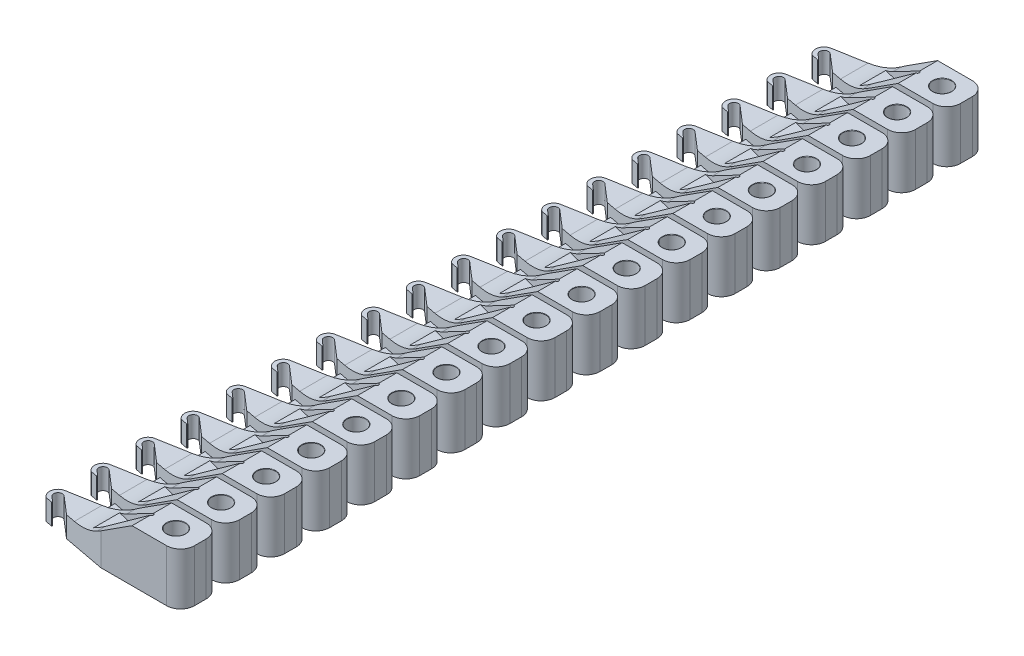
SolidWorks part; units mm, degrees
ref_plane "Front Plane" through (0, 0, 0) normal (0, 0, 1) x (1, 0, 0)
ref_plane "Top Plane" through (0, 0, 0) normal (0, 1, 0) x (1, 0, 0)
ref_plane "Right Plane" through (0, 0, 0) normal (1, 0, 0) x (0, 0, -1)
sketch "Sketch1" plane through (0, 0, 0) normal (0, 1, 0) x (1, 0, 0)
  line L0 (0.7, 0.57) -> (-1.6, 0.57)
  line L1 (0.7, 0.57) -> (0.7, -0.57)
  line L2 (0.7, -0.57) -> (-1.6, -0.57)
  line L3 (-1.6, 0.57) -> (-3.681, 0.2)
  line L4 (-3.4049, 0) -> (-2.2666, -0.982) construction
  line L5 (-1.6, -0.57) -> (-3.7439, -0.166)
  line L6 (0, 0) -> (-4.3932, 0) construction
  line L7 (-3.3232, 0.0948) -> (-2.1848, -0.8872)
  line L8 (-3.4867, -0.0948) -> (-2.3484, -1.0768)
  line L9 (-3.341, 0) -> (-3.341, -0.5283)
  line L13 (1.2, 1.1) -> (1.2, -1.1)
  circle A0 centre (0, 0) radius 0.27
  circle A1 centre (-3.7, 0) radius 0.1717
  arc A2 (-3.3232, 0.0948) -> (-3.4867, -0.0948) centre (-3.4049, 0) ccw
  arc A3 (-2.3484, -1.0768) -> (-2.1848, -0.8872) centre (-2.2666, -0.982) ccw
  circle A4 centre (-3.4049, 0) radius 0.2452
  point P13 (-2.8358, -0.491)
  dimension "D1" = 0.57
  dimension "D9" = 0.54
  dimension "D2" = 0.57
  dimension "D3" = 0.7
  dimension "D4" = 1.6
  dimension "D5" = 1.6
  dimension "D6" = 0.2
  dimension "D12" = 0.5
extrude "Boss-Extrude1" add sketch "Sketch1" along normal blind 1.5
pattern_linear "LPattern1" [suppressed] count 9 spacing 3.2 count 4 spacing 6.2
sketch "Sketch2" plane through (0, 0, 0) normal (0, 0, 1) x (1, 0, 0)
  line L0 (-4.2545, 0.6) -> (-2.1, 0.6)
  line L1 (-2.1, 0.6) -> (-0.7, 1.5)
  line L2 (-0.7, 1.5) -> (-4.2545, 1.5)
  line L3 (-4.2545, 1.5) -> (-4.2545, 0.6)
  line L4 (0.7, 1.5) -> (0.7, 0) construction
  line L5 (-1.6, 0) -> (-2.8188, 0) construction
  dimension "D1" = 0.6
  dimension "D2" = 1.4
  dimension "D3" = 2.8
extrude "Cut-Extrude1" cut sketch "Sketch2" against normal through all and the other way through all
fillet "Fillet1" radius 0.01 2 edges at (0, 1.5, 0.27) (0, 0, 0.27)
fillet "Fillet2" radius 1.5 1 edges at (-2.1, 0.6, -0.0027)
fillet "Fillet3" radius 0.4 2 edges at (0.7, 0.75, -0.57) (0.7, 0.75, 0.57)
sketch "Sketch4" plane through (0, 1.5, 0) normal (0, 1, 0) x (1, 0, 0)
  line L0 (-0.5, 0) -> (-2.5, 0.5)
  line L2 (-2.5, 0.5) -> (-2.5, -0.5)
  line L3 (-2.5, -0.5) -> (-0.5, 0)
  point P2 (-0.5382, 0)
  point P4 (-0.7, 0)
  dimension "D1" = 0.5
  dimension "D2" = 0.5
  dimension "D3" = 0.5
  dimension "D4" = 2.5
extrude "Cut-Extrude2" cut sketch "Sketch4" against normal blind 0.8
fillet "Fillet4" radius 0.05 1 edges at (-0.5, 1.1, 0)
pattern_linear "LPattern2" count 18 spacing 1.3 along (0, 0, -1) of bodies 134 103
sketch "Sketch3" plane through (0, 0, 0) normal (0, 0, 1) x (1, 0, 0)
  line L1 (-2.7, 0.3) -> (-2, 0.3)
  line L2 (-2.7, 0.3) -> (-2.7, 0)
  line L3 (-2.7, 0) -> (-2, 0)
  line L4 (-2, 0.3) -> (-2, 0)
  dimension "D1" = 0.3
  dimension "D3" = 0.7
  dimension "D4" = 2
extrude "Boss-Extrude2" add sketch "Sketch3" against normal up to surface (22.5989 mm away)
